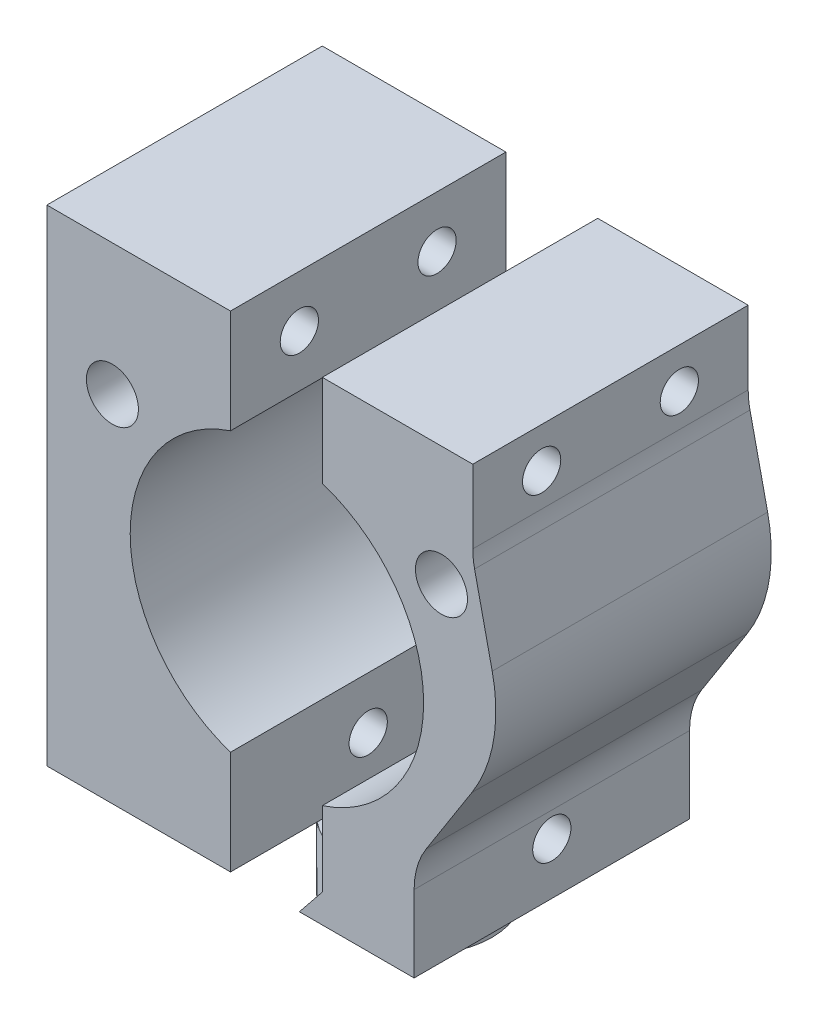
SolidWorks part; units mm, degrees
material "Plain Carbon Steel"
ref_plane "Front Plane" through (0, 0, 0) normal (0, 0, 1) x (1, 0, 0)
ref_plane "Top Plane" through (0, 0, 0) normal (0, 1, 0) x (1, 0, 0)
ref_plane "Right Plane" through (0, 0, 0) normal (1, 0, 0) x (0, 0, -1)
sketch "Sketch1" plane through (0, 0, 0) normal (0, 1, 0) x (1, 0, 0)
  line L0 (0, 4.75) -> (0, -4.75) construction
  line L1 (1.5, 4.5069) -> (1.5, -4.5069)
  line L2 (-1.5, 4.5069) -> (-1.5, -4.5069)
  circle A0 centre (0, 0) radius 4.75
  dimension "D1" = 9.5
  dimension "D2" = 1.5
ref_plane "GroundPlane" through (0, 4.5, 0) normal (0, 1, 0) x (-1, 0, 0)
sketch "Sketch2" plane through (0, 4.5, 0) normal (0, 1, 0) x (-1, 0, 0)
  line L0 (0, 7.5) -> (6.4952, -3.75) construction
  line L1 (0, 7.5) -> (0, -7.5) construction
  line L2 (0, 12.7) -> (0, -12.7) construction
  line L3 (0, 7.5) -> (-6.4952, -3.75) construction
  line L4 (-9.2393, -11.2686) -> (9.8107, -11.2686) construction
  line L5 (-9.2393, -11.2686) -> (-9.2393, -30.3186) construction
  line L6 (-9.2393, -30.3186) -> (9.8107, -30.3186) construction
  line L7 (9.8107, -11.2686) -> (9.8107, -30.3186) construction
  line L8 (-6.4952, -3.75) -> (6.4952, -3.75) construction
  line L9 (0, -7.5) -> (6.4952, 3.75) construction
  line L10 (6.4952, 3.75) -> (-6.4952, 3.75) construction
  line L11 (-6.4952, 3.75) -> (0, -7.5) construction
  line L12 (3, -8.6561) -> (3, 9.3439)
  line L13 (3, -8.6561) -> (15, -8.6561)
  line L14 (3, 9.3439) -> (15, 9.3439)
  line L15 (15, 9.3439) -> (15, -8.6561)
  line L16 (-3, -8.6561) -> (-3, 9.3439)
  line L17 (-3, -8.6561) -> (-15, -8.6561)
  line L18 (-3, 9.3439) -> (-15, 9.3439)
  line L19 (-15, 9.3439) -> (-15, -8.6561)
  circle A0 centre (0, 0) radius 7.5 construction
  dimension "D1" = 15
  dimension "D2" = 30
  dimension "D3" = 25.4
  dimension "D4" = 19.05
  dimension "D5" = 19.05
  dimension "D6" = 30
  dimension "D7" = 30
  dimension "D8" = 3
  dimension "D9" = 18
  dimension "D10" = 12
ref_plane "TopPlane" through (0, 36.25, 0) normal (0, 1, 0) x (-1, 0, 0)
extrude "Extrude1" add sketch "Sketch2" along normal blind 31.75
extrude "Extrude2" add sketch "Sketch1" along normal blind 4.5 contours L1 A0 | L2 A0
sketch "Sketch4" plane through (0, 0, 9.3439) normal (0, 0, 1) x (1, 0, 0)
  line L0 (-14.9586, 36.25) -> (15.0262, 4.5) construction
  line L1 (9.9, 36.25) -> (-9.9, 36.25) construction
  line L2 (9.9, 4.5) -> (-9.9, 4.5) construction
  line L3 (15.0262, 36.25) -> (-14.9586, 4.5) construction
  circle A0 centre (0.0338, 20.375) radius 9.5885
  point P8 (0.0338, 20.375)
  dimension "D1" = 19.177
extrude "Magnet Cavity" cut sketch "Sketch4" against normal through all
sketch "Sketch6" plane through (15, 0, 0) normal (1, 0, 0) x (0, 0, -1)
  line L0 (-9.3439, 36.25) -> (-9.3439, 4.5) construction
  line L1 (-9.3439, 20.375) -> (8.6561, 20.375) construction
  line L2 (8.6561, 36.25) -> (8.6561, 4.5) construction
  line L3 (-0.3439, 36.25) -> (-0.3439, 4.5) construction
  line L4 (-9.3439, 36.25) -> (8.6561, 36.25) construction
  line L5 (-9.3439, 4.5) -> (8.6561, 4.5) construction
  line L6 (-0.3439, 36.25) -> (-9.3439, 29.4932) construction
  point P12 (-4.8439, 32.8716)
  point P15 (4.1561, 32.8716)
  point P16 (4.1561, 7.8784)
  point P17 (-4.8439, 7.8784)
  point P18 (-0.3439, 32.8716)
  point P19 (-0.3439, 7.8784)
sketch "Mount Hole circle" plane through (0, 0, 9.3439) normal (0, 0, 1) x (1, 0, 0)
  line L0 (0.0338, 20.375) -> (0.0338, 33.375) construction
  line L1 (0.0338, 20.375) -> (10.786, 27.6817) construction
  line L2 (0.0338, 20.375) -> (-10.7185, 27.6817) construction
  circle A0 centre (0.0338, 20.375) radius 13 construction
  dimension "D1" = 26
  dimension "D2" = 55.802
sketch "Sketch14" plane through (0, 4.5, 0) normal (0, 1, 0) x (-1, 0, 0)
  point P0 (6.4952, 3.75)
  point P1 (-6.4952, 3.75)
  point P3 (0, -7.5)
sketch "Sketch16" plane through (0, 4.5, 0) normal (0, 1, 0) x (-1, 0, 0)
  point P0 (6.4952, 3.75)
  point P1 (-6.4952, 3.75)
  point P3 (0, -7.5)
hole_wizard "M3x0.5 Tapped Hole1" positions "3DSketch3" profile "Sketch18" tap size "M3x0.5" standard "Ansi Metric" end condition through all
sketch3d "3DSketch3"
  point P0 (15, 32.8716, 4.8439)
  point P3 (15, 32.8716, -4.1561)
  point P6 (15, 7.8784, 0.3439)
sketch "Sketch18" plane through (15, 32.8716, 4.8439) normal (0, 1, 0) x (0, 0, -1)
  line L0 (0, 0) -> (0, 30)
  line L1 (0, 30) -> (1.25, 30)
  line L2 (1.25, 30) -> (1.25, 0)
  line L5 (1.25, 0) -> (0, 0)
  line L11 (0, -6.35) -> (0, 107.95) construction
  dimension "Thru Tap Drill Dia." = 2.5
  dimension "Thru Tap Drill Depth" = 30
cosmetic thread "Hole Thread6" parameters "D2"=3
cosmetic thread "Hole Thread7" parameters "D2"=3
cosmetic thread "Hole Thread8" parameters "D2"=3
hole_wizard "M2x0.4 Tapped Hole2" positions "3DSketch8" profile "Sketch23" tap size "M2x0.4" standard "Ansi Metric"
sketch3d "3DSketch8"
  point P9 (-6.4952, 4.5, 3.75)
  point P11 (6.4952, 4.5, 3.75)
sketch "Sketch23" plane through (-6.4952, 4.5, 3.75) normal (1, 0, 0) x (0, 0, -1)
  line L0 (0, 0) -> (0, 6.4807)
  line L1 (0, 6.4807) -> (0.8, 6)
  line L2 (0.8, 6) -> (0.8, 0)
  line L5 (0.8, 0) -> (0, 0)
  line L10 (0, 6.4807) -> (-0.8, 6) construction
  line L11 (0, -6.35) -> (0, 107.95) construction
  dimension "Tap Drill Dia." = 1.6
  dimension "Tap Drill Depth" = 6
  dimension "Drill Angle" = 118
cosmetic thread "Hole Thread16" parameters "D1"=4, "D2"=2
cosmetic thread "Hole Thread17" parameters "D1"=4, "D2"=2
hole_wizard "M3 Clearance Hole1" positions "3DSketch9" profile "Sketch24" hole size "M3" standard "Ansi Metric"
sketch3d "3DSketch9"
  point P0 (-10.7185, 27.6817, 9.3439)
  point P3 (10.786, 27.6817, 9.3439)
sketch "Sketch24" plane through (-10.7185, 27.6817, 9.3439) normal (1, 0, 0) x (0, -1, 0)
  line L0 (0, 0) -> (0, 19.0215)
  line L1 (0, 19.0215) -> (1.7, 18)
  line L2 (1.7, 18) -> (1.7, 0)
  line L5 (1.7, 0) -> (0, 0)
  line L10 (0, 19.0215) -> (-1.7, 18) construction
  line L11 (0, -6.35) -> (0, 107.95) construction
  dimension "Hole Dia." = 3.4
  dimension "Hole Depth" = 18
  dimension "Drill Angle" = 118
sketch "Trim Sketch" plane through (0, 0, 9.3439) normal (0, 0, 1) x (1, 0, 0)
  line L0 (9, 4.5) -> (9, 9.5039)
  line L1 (3, 4.5) -> (15, 4.5) construction
  line L2 (9.7837, 12.1914) -> (12.7736, 16.8821)
  line L3 (15, 36.25) -> (15, 4.5) construction
  line L4 (14.1045, 24.4192) -> (12.9518, 29.6242)
  line L5 (12.8336, 30.7052) -> (12.8336, 35.4975)
  line L6 (12.8336, 35.4975) -> (3, 35.4975)
  line L7 (3, 36.25) -> (3, 29.4932) construction
  line L8 (0.0338, 33.375) -> (0, 0) construction
  line L9 (-8.9909, 4.5182) -> (-8.9808, 9.5221)
  line L10 (-9.759, 12.2112) -> (-12.7394, 16.9079)
  line L11 (-14.055, 24.4477) -> (-12.8919, 29.6503)
  line L12 (-12.7714, 30.7311) -> (-12.7617, 35.5234)
  line L13 (-12.7617, 35.5234) -> (-2.9282, 35.5035)
  circle A0 centre (0.0338, 20.375) radius 13 construction
  arc A1 (12.9518, 29.6242) -> (12.8336, 30.7052) centre (17.8336, 30.7052) cw
  arc A2 (12.7736, 16.8821) -> (14.1045, 24.4192) centre (4.341, 22.2571) ccw
  arc A3 (9.7837, 12.1914) -> (9, 9.5039) centre (14, 9.5039) ccw
  arc A4 (-9.759, 12.2112) -> (-8.9808, 9.5221) centre (-13.9807, 9.5322) cw
  arc A5 (-12.7394, 16.9079) -> (-14.055, 24.4477) centre (-4.2959, 22.2659) cw
  arc A6 (-12.8919, 29.6503) -> (-12.7714, 30.7311) centre (-17.7714, 30.7412) ccw
  point P18 (15, 20.375)
  point P21 (9, 10.9619)
  line M2 (3, 36.25) -> (3, 29.4932)
  line M5 (3, 4.5) -> (15, 4.5)
  line M6 (15, 4.5) -> (15, 36.25)
  line M7 (15, 36.25) -> (3, 36.25)
  dimension "D1" = 5
  dimension "D2" = 10
  dimension "D3" = 5
extrude "Extrude3" cut sketch "Trim Sketch" against normal through all contours L2 A3 L0 L6 L5 A1 L4 A2 M5 M6 M7 M2
sketch "Sketch26" plane through (0, 0, 9.3439) normal (0, 0, 1) x (1, 0, 0)
  line L0 (1.5, 4.5) -> (3, 6.36)
  line L1 (3, 11.2568) -> (3, 4.5) construction
  line L2 (1.5, 4.5) -> (3, 4.5)
  line L3 (3, 4.5) -> (3, 6.36)
extrude "Extrude4" add sketch "Sketch26" against normal up to surface (18 mm away) up to face at (12.486, 27.6817, -8.6561)
